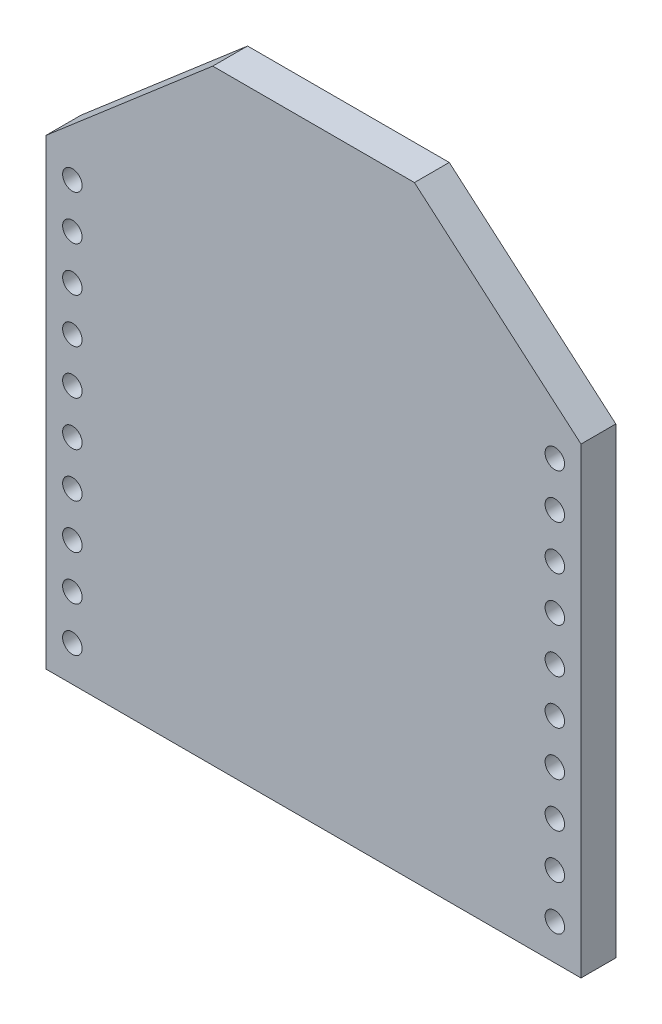
SolidWorks part; units mm, degrees
ref_plane "Plane1" through (0, 0, 0) normal (0, 0, 1) x (1, 0, 0)
ref_plane "Plane2" through (0, 0, 0) normal (0, 1, 0) x (1, 0, 0)
ref_plane "Plane3" through (0, 0, 0) normal (1, 0, 0) x (0, 0, -1)
sketch "Sketch1" plane through (0, 0, 0) normal (0, 0, 1) x (1, 0, 0)
  line L0 (12.192, 0) -> (-12.192, 0)
  line L1 (-12.192, 0) -> (-12.192, 21.082)
  line L2 (-12.192, 21.082) -> (-4.5974, 27.6098)
  line L3 (-4.5974, 27.6098) -> (4.5974, 27.6098)
  line L4 (0, 27.6098) -> (0, 0) construction
  line L5 (12.192, 21.082) -> (4.5974, 27.6098)
  line L6 (12.192, 0) -> (12.192, 21.082)
  line L7 (-10.9982, 19.9166) -> (-10.9982, 1.6286) construction
  line L8 (10.9982, 19.9166) -> (10.9982, 1.6286) construction
  circle A0 centre (-10.9982, 1.6286) radius 0.4445
  circle A1 centre (-10.9982, 3.6606) radius 0.4445
  circle A2 centre (-10.9982, 5.6926) radius 0.4445
  circle A3 centre (-10.9982, 7.7246) radius 0.4445
  circle A4 centre (-10.9982, 9.7566) radius 0.4445
  circle A5 centre (-10.9982, 11.7886) radius 0.4445
  circle A6 centre (-10.9982, 13.8206) radius 0.4445
  circle A7 centre (-10.9982, 15.8526) radius 0.4445
  circle A8 centre (-10.9982, 17.8846) radius 0.4445
  circle A9 centre (-10.9982, 19.9166) radius 0.4445
  circle A10 centre (10.9982, 19.9166) radius 0.4445
  circle A11 centre (10.9982, 17.8846) radius 0.4445
  circle A12 centre (10.9982, 15.8526) radius 0.4445
  circle A13 centre (10.9982, 13.8206) radius 0.4445
  circle A14 centre (10.9982, 11.7886) radius 0.4445
  circle A15 centre (10.9982, 9.7566) radius 0.4445
  circle A16 centre (10.9982, 7.7246) radius 0.4445
  circle A17 centre (10.9982, 5.6926) radius 0.4445
  circle A18 centre (10.9982, 3.6606) radius 0.4445
  circle A19 centre (10.9982, 1.6286) radius 0.4445
  dimension "D5" = 0.889
  dimension "D1" = 24.384
  dimension "D2" = 27.6098
  dimension "D3" = 6.5278
  dimension "D4" = 7.5946
  dimension "D7" = 21.9964
  dimension "D8" = 2.032
  dimension "D6" = 10
extrude "Boss-Extrude1" add sketch "Sketch1" along normal blind 1.5875
